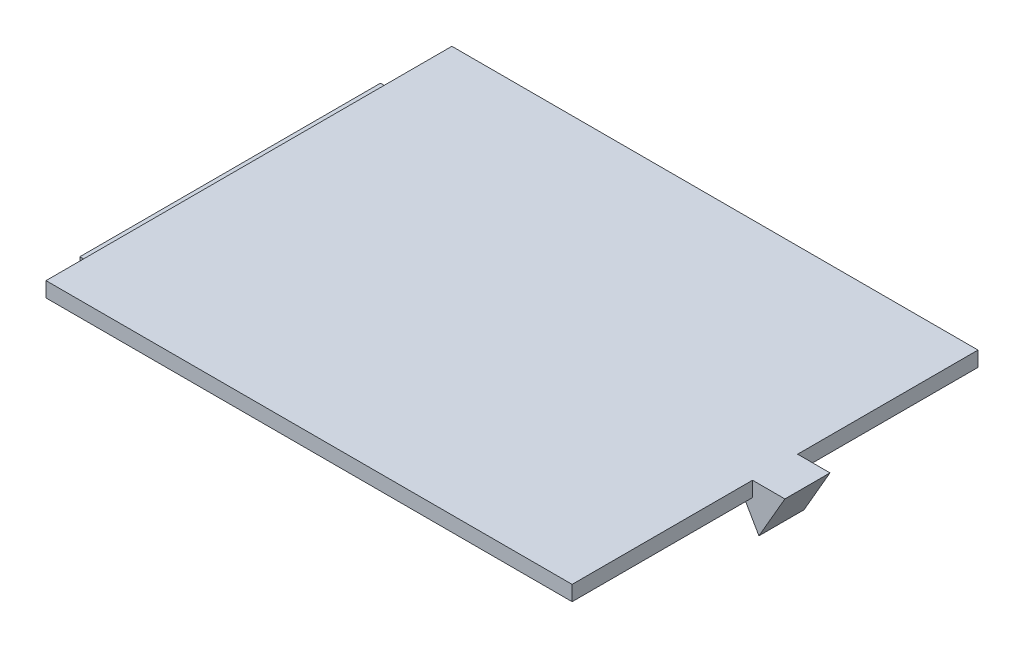
SolidWorks part; units mm, degrees
ref_plane "Front Plane" through (0, 0, 0) normal (0, 0, 1) x (1, 0, 0)
ref_plane "Top Plane" through (0, 0, 0) normal (0, 1, 0) x (1, 0, 0)
ref_plane "Right Plane" through (0, 0, 0) normal (1, 0, 0) x (0, 0, -1)
sketch "Sketch1" plane through (0, 0, 0) normal (0, 1, 0) x (1, 0, 0)
  line L1 (-35, -27) -> (35, -27)
  line L2 (-35, -27) -> (-35, 27)
  line L3 (-35, 27) -> (35, 27)
  line L4 (35, -27) -> (35, 27)
  line L5 (-35, -27) -> (35, 27) construction
  line L6 (-35, 27) -> (35, -27) construction
  point P0 (0, 0)
  dimension "D1" = 54
  dimension "D2" = 70
extrude "Boss-Extrude1" add sketch "Sketch1" along normal blind 2
sketch "Sketch2" plane through (0, 0, 0) normal (0, -1, 0) x (1, 0, 0)
  line L0 (-35, -27) -> (-35, 27) construction
  line L1 (-37.5, -20) -> (-32.5, -20)
  line L2 (-37.5, -20) -> (-37.5, 20)
  line L3 (-37.5, 20) -> (-32.5, 20)
  line L4 (-32.5, -20) -> (-32.5, 20)
  line L5 (-37.5, -20) -> (-32.5, 20) construction
  line L6 (-37.5, 20) -> (-32.5, -20) construction
  point P0 (-35, 0)
  dimension "D1" = 40
  dimension "D2" = 5
extrude "Boss-Extrude2" add sketch "Sketch2" along normal blind 1
sketch "Sketch3" plane through (0, 0, 27) normal (0, 0, 1) x (1, 0, 0)
  line L0 (-35, 2) -> (35, 2) construction
  line L1 (35.8546, -3.9815) -> (39.308, 2)
  line L2 (39.308, 2) -> (32.4012, 2)
  line L3 (32.4012, 2) -> (35.8546, -3.9815)
  circle A0 centre (35.8546, 0.0062) radius 1.9938 construction
  point P1 (37.0122, -1.0598)
  point P9 (35.8546, -3.9815)
extrude "Boss-Extrude3" add sketch "Sketch3" against normal blind 6 from offset 24
